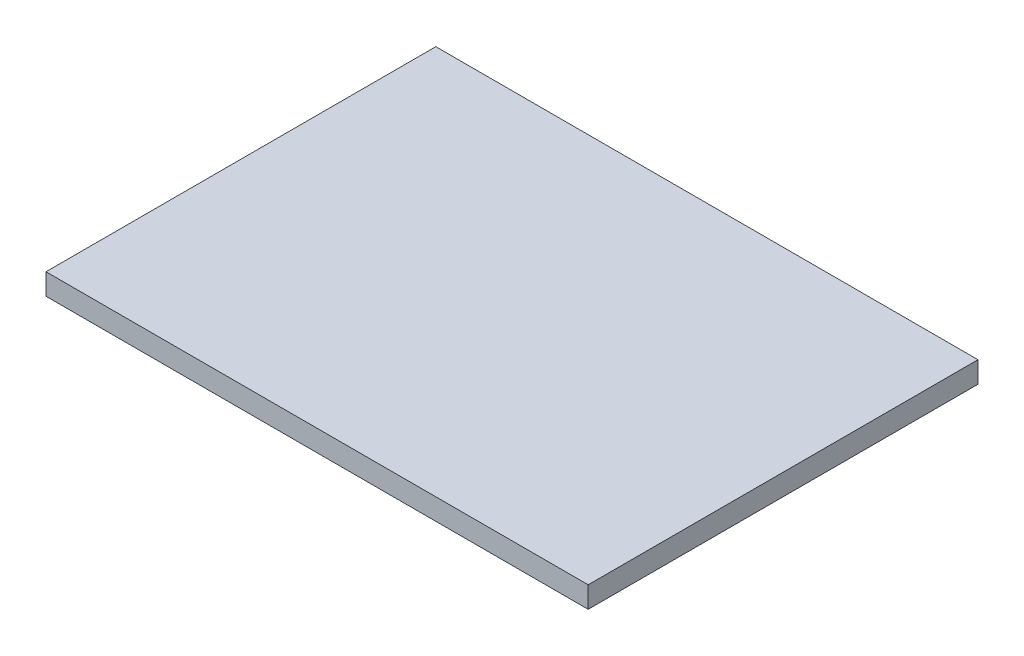
SolidWorks part; units mm, degrees
ref_plane "Front Plane" through (0, 0, 0) normal (0, 0, 1) x (1, 0, 0)
ref_plane "Top Plane" through (0, 0, 0) normal (0, 1, 0) x (1, 0, 0)
ref_plane "Right Plane" through (0, 0, 0) normal (1, 0, 0) x (0, 0, -1)
sketch "Sketch1" plane through (0, 0, 0) normal (0, 1, 0) x (1, 0, 0)
  line L22 (102, 15) -> (255, 15)
  line L23 (255, 15) -> (255, 125)
  line L26 (102, 125) -> (255, 125)
  line L30 (102, 125) -> (102, 15)
extrude "Boss-Extrude1" add sketch "Sketch1" along normal blind 6
